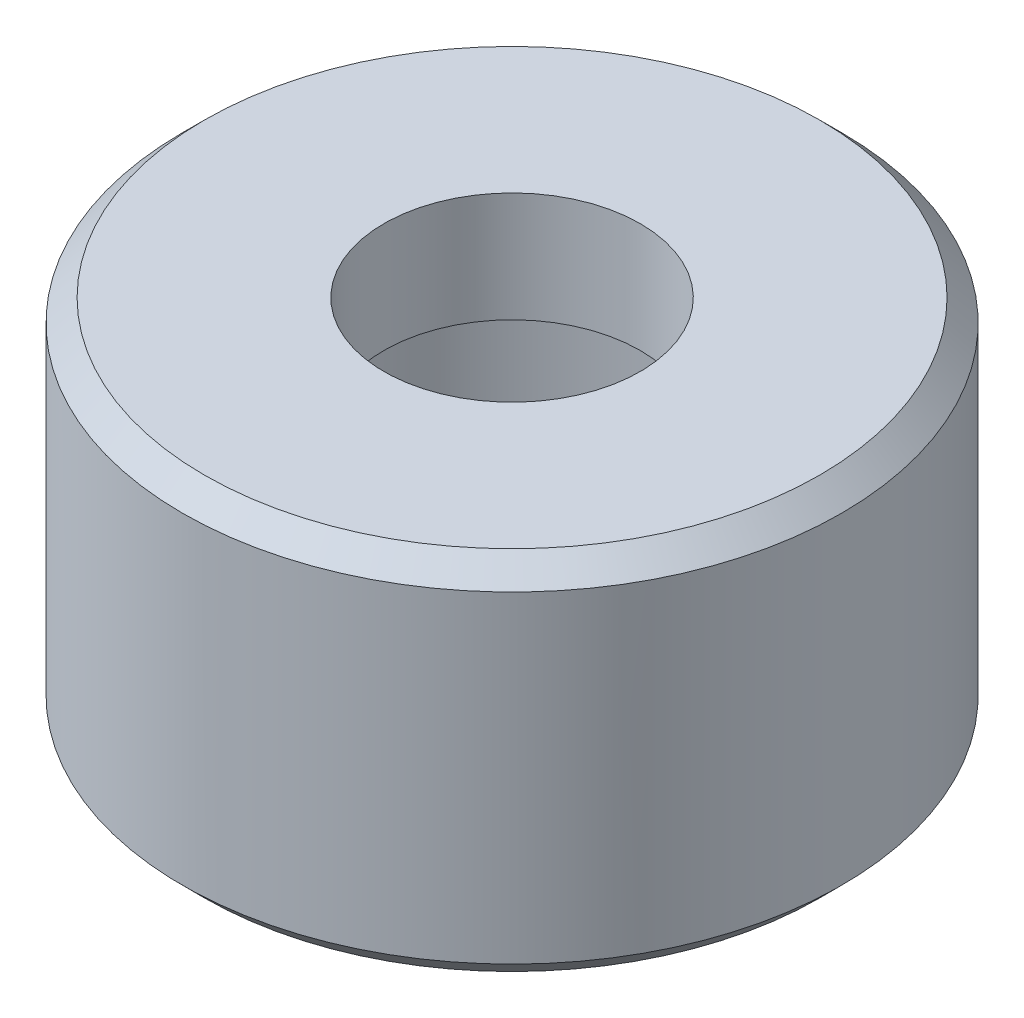
SolidWorks part; units mm, degrees
ref_plane "Front Plane" through (0, 0, 0) normal (0, 0, 1) x (1, 0, 0)
ref_plane "Top Plane" through (0, 0, 0) normal (0, 1, 0) x (1, 0, 0)
ref_plane "Right Plane" through (0, 0, 0) normal (1, 0, 0) x (0, 0, -1)
sketch "Sketch2" plane through (0, 0, 0) normal (1, 0, 0) x (0, 0, -1)
  line L0 (0, 0) -> (0, 14.71) construction
  line L1 (1.75, 5) -> (1.75, 3.5)
  line L2 (1.75, 3.5) -> (3, 3.5)
  line L3 (3, 3.5) -> (3, 0)
  line L4 (3, 0) -> (4.5, 0)
  line L5 (4.5, 0) -> (4.5, 5)
  line L6 (4.5, 5) -> (1.75, 5)
  dimension "D1" = 6
  dimension "D2" = 3.5
  dimension "D3" = 3.5
  dimension "D4" = 5
  dimension "D5" = 9
revolve "Revolve1" add sketch "Sketch2" angle 360 about L0
chamfer "Chamfer1" distance 0.3 angle 45 2 edges at (0, 0, -4.5) (0, 5, -4.5)
